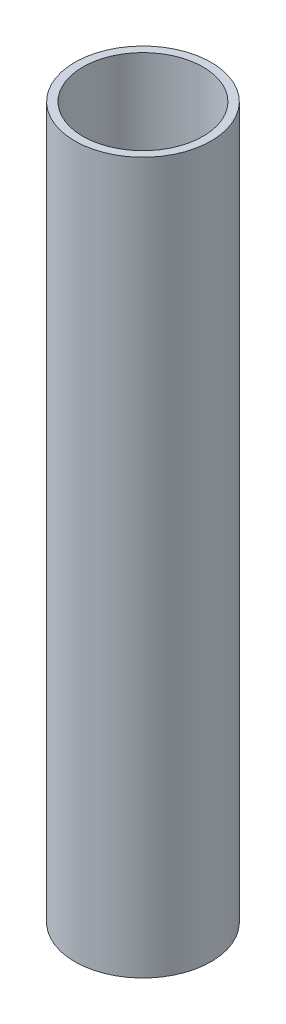
SolidWorks part; units mm, degrees
material "1060 Alloy"
ref_plane "Front Plane" through (0, 0, 0) normal (0, 0, 1) x (1, 0, 0)
ref_plane "Top Plane" through (0, 0, 0) normal (0, 1, 0) x (1, 0, 0)
ref_plane "Right Plane" through (0, 0, 0) normal (1, 0, 0) x (0, 0, -1)
sketch "Sketch1" plane through (0, 0, 0) normal (0, 1, 0) x (1, 0, 0)
  circle A0 centre (0, 0) radius 25.2
  circle A1 centre (0, 0) radius 28.575
  dimension "D1" = 57.15
  dimension "D2" = 50.4
extrude "Boss-Extrude1" add sketch "Sketch1" along normal mid plane 298
